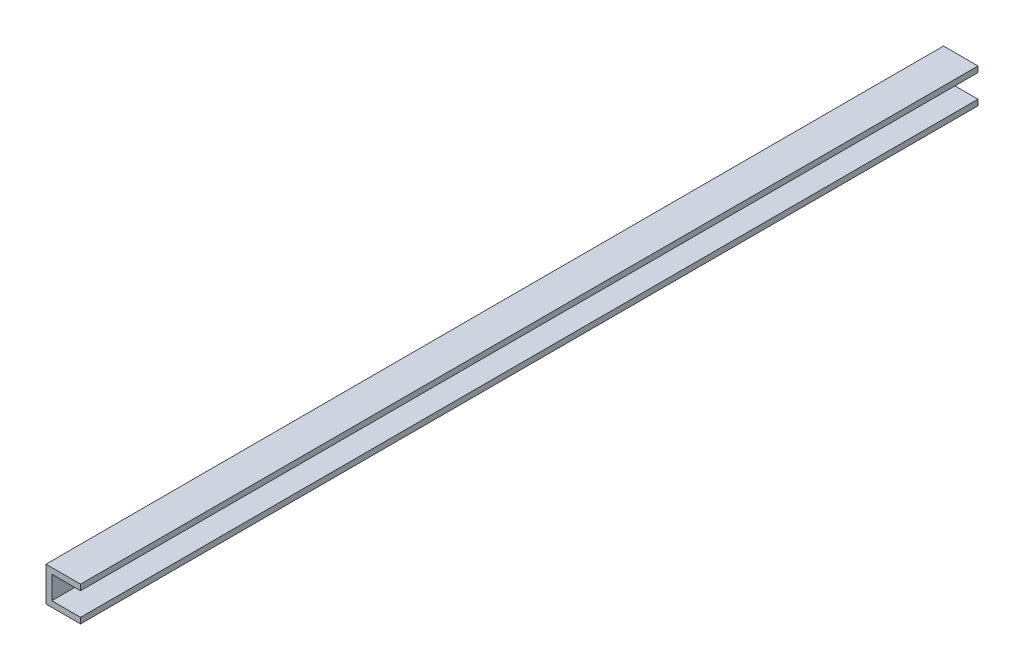
SolidWorks part; units mm, degrees
material "6063-T6"
ref_plane "Front Plane" through (0, 0, 0) normal (0, 0, 1) x (1, 0, 0)
ref_plane "Top Plane" through (0, 0, 0) normal (0, 1, 0) x (1, 0, 0)
ref_plane "Right Plane" through (0, 0, 0) normal (1, 0, 0) x (0, 0, -1)
sketch "Sketch1" plane through (0, 0, 0) normal (0, 0, 1) x (1, 0, 0)
  line L0 (0, 4.7625) -> (0, -4.7625)
  line L1 (0, 4.7625) -> (9.525, 4.7625)
  line L2 (9.525, 4.7625) -> (9.525, 3.175)
  line L3 (9.525, 3.175) -> (1.5875, 3.175)
  line L4 (1.5875, 3.175) -> (1.5875, -3.175)
  line L5 (0, 0) -> (28.1303, 0) construction
  line L6 (0, -4.7625) -> (9.525, -4.7625)
  line L7 (9.525, -4.7625) -> (9.525, -3.175)
  line L8 (9.525, -3.175) -> (1.5875, -3.175)
  point P12 (1.5875, 0)
  dimension "D1" = 9.525
  dimension "D2" = 9.525
  dimension "D3" = 1.5875
  dimension "D4" = 1.5875
extrude "Boss-Extrude1" add sketch "Sketch1" along normal mid plane 247.65
hole_wizard "CSK for #6 Flat Head Machine Screw (100)1" [suppressed] positions "Sketch9" profile "Sketch8" countersink size "#6" standard "ANSI Inch"
sketch "Sketch9" plane through (1.5875, 0, 0) normal (1, 0, 0) x (0, 0, -1)
  line L0 (0, 0) -> (0, 52.5523) construction
  point P0 (0, 0)
  point P4 (-152.4, 0)
  point P11 (152.4, 0)
  dimension "D1" = 152.4
sketch "Sketch8" plane through (1.5875, 0, 0) normal (0, 1, 0) x (0, 0, -1)
  line L0 (0, 0) -> (0, 1.5875)
  line L1 (0, 1.5875) -> (1.8986, 1.5875)
  line L2 (1.8986, 1.5875) -> (1.8986, 1.38)
  line L3 (1.8986, 1.38) -> (3.5433, 0)
  line L5 (3.5433, 0) -> (0, 0)
  line L6 (-1.8986, 1.38) -> (-3.5433, 0) construction
  line L11 (0, -6.35) -> (0, 107.95) construction
  dimension "Thru Hole Dia." = 3.7973
  dimension "Thru Hole Depth" = 1.5875
  dimension "Near C'Sink Dia." = 7.0866
  dimension "Near C'Sink Angle" = 100
sketch "Sketch10" [suppressed] plane through (0, 0, 0) normal (-1, 0, 0) x (0, 0, 1)
  line L0 (-152.4, 0) -> (0, 0) construction
  line L1 (-76.2, 0) -> (-76.2, 55.5365) construction
  line L2 (0, 0) -> (0, -71.488) construction
  circle A0 centre (-114.3, 0) radius 1.27
  circle A1 centre (-38.1, 0) radius 1.27
  circle A2 centre (38.1, 0) radius 1.27
  circle A3 centre (114.3, 0) radius 1.27
  dimension "D1" = 2.54
  dimension "D2" = 76.2
extrude "Cut-Extrude1" [suppressed] cut sketch "Sketch10" against normal through all
sketch "Sketch11" plane through (0, 0, 0) normal (-1, 0, 0) x (0, 0, 1)
  line L0 (-123.825, 4.7625) -> (-123.825, -4.7625) construction
  line L1 (-119.6975, -2.3812) -> (-121.285, -2.3812)
  line L2 (-119.6975, -2.3812) -> (-119.6975, 2.3813)
  line L3 (-119.6975, 2.3813) -> (-121.285, 2.3813)
  line L4 (-121.285, -2.3812) -> (-121.285, 2.3813)
  line L5 (-119.6975, -2.3812) -> (-121.285, 2.3813) construction
  line L6 (-119.6975, 2.3813) -> (-121.285, -2.3812) construction
  line L7 (123.825, -4.7625) -> (-123.825, -4.7625) construction
  line L8 (123.825, 4.7625) -> (-123.825, 4.7625) construction
  line L9 (-117.3162, 4.7625) -> (-117.3162, -4.7625) construction
  line L10 (-114.935, -2.3812) -> (-113.3475, -2.3812)
  line L11 (-113.3475, -2.3812) -> (-113.3475, 2.3813)
  line L12 (-114.935, 2.3813) -> (-113.3475, 2.3813)
  line L13 (-114.935, -2.3812) -> (-114.935, 2.3813)
  point P0 (-120.4912, 0)
  dimension "D1" = 2.54
  dimension "D2" = 2.3813
  dimension "D3" = 2.3813
  dimension "D4" = 1.5875
  dimension "D5" = 2.3813
extrude "Cut-Extrude2" cut sketch "Sketch11" against normal through all
hole_wizard "#6-32 Tapped Hole1" positions "Sketch14" profile "Sketch13" tap size "#6-32" standard "ANSI Inch"
sketch "Sketch14" plane through (0, 0, 0) normal (-1, 0, 0) x (0, 0, 1)
  line L0 (-100.6475, 0) -> (123.825, 0) construction
  line L1 (123.825, 4.7625) -> (123.825, -4.7625) construction
  line L2 (-113.3475, -2.3812) -> (-113.3475, 2.3813) construction
  point P1 (-100.6475, 0)
  point P31 (-87.8086, 0)
  point P32 (-74.9697, 0)
  point P33 (-62.1308, 0)
  point P34 (-49.2919, 0)
  point P35 (-36.453, 0)
  point P36 (-23.6141, 0)
  point P37 (-10.7752, 0)
  point P38 (2.0637, 0)
  point P39 (14.9027, 0)
  point P40 (27.7416, 0)
  point P41 (40.5805, 0)
  point P42 (53.4194, 0)
  point P43 (66.2583, 0)
  point P44 (79.0972, 0)
  point P45 (91.9361, 0)
  point P58 (104.775, 0) [skipped]
  dimension "D2" = 12.7
  dimension "D1" = 17
sketch "Sketch13" plane through (0, 0, -100.6475) normal (0, 1, 0) x (0, 0, 1)
  line L0 (0, 0) -> (0, 9.398)
  line L1 (0, 9.398) -> (1.3525, 9.398)
  line L2 (1.3525, 9.398) -> (1.3525, 0)
  line L5 (1.3525, 0) -> (0, 0)
  line L10 (0, 9.398) -> (-1.3525, 9.398) construction
  line L11 (0, -6.35) -> (0, 107.95) construction
  dimension "Tap Drill Dia." = 2.7051
  dimension "Tap Drill Depth" = 9.398
  dimension "Drill Angle" = 180
cosmetic thread "Hole Thread2" parameters "D1"=1.5875, "D2"=3.5052
cosmetic thread "Hole Thread3" parameters "D1"=1.5875, "D2"=3.5052
cosmetic thread "Hole Thread4" parameters "D1"=1.5875, "D2"=3.5052
cosmetic thread "Hole Thread5" parameters "D1"=1.5875, "D2"=3.5052
cosmetic thread "Hole Thread6" parameters "D1"=1.5875, "D2"=3.5052
cosmetic thread "Hole Thread7" parameters "D1"=1.5875, "D2"=3.5052
cosmetic thread "Hole Thread8" parameters "D1"=1.5875, "D2"=3.5052
cosmetic thread "Hole Thread9" parameters "D1"=1.5875, "D2"=3.5052
cosmetic thread "Hole Thread10" parameters "D1"=1.5875, "D2"=3.5052
cosmetic thread "Hole Thread11" parameters "D1"=1.5875, "D2"=3.5052
cosmetic thread "Hole Thread12" parameters "D1"=1.5875, "D2"=3.5052
cosmetic thread "Hole Thread13" parameters "D1"=1.5875, "D2"=3.5052
cosmetic thread "Hole Thread14" parameters "D1"=1.5875, "D2"=3.5052
cosmetic thread "Hole Thread15" parameters "D1"=1.5875, "D2"=3.5052
cosmetic thread "Hole Thread16" parameters "D1"=1.5875, "D2"=3.5052
cosmetic thread "Hole Thread17" parameters "D1"=1.5875, "D2"=3.5052
